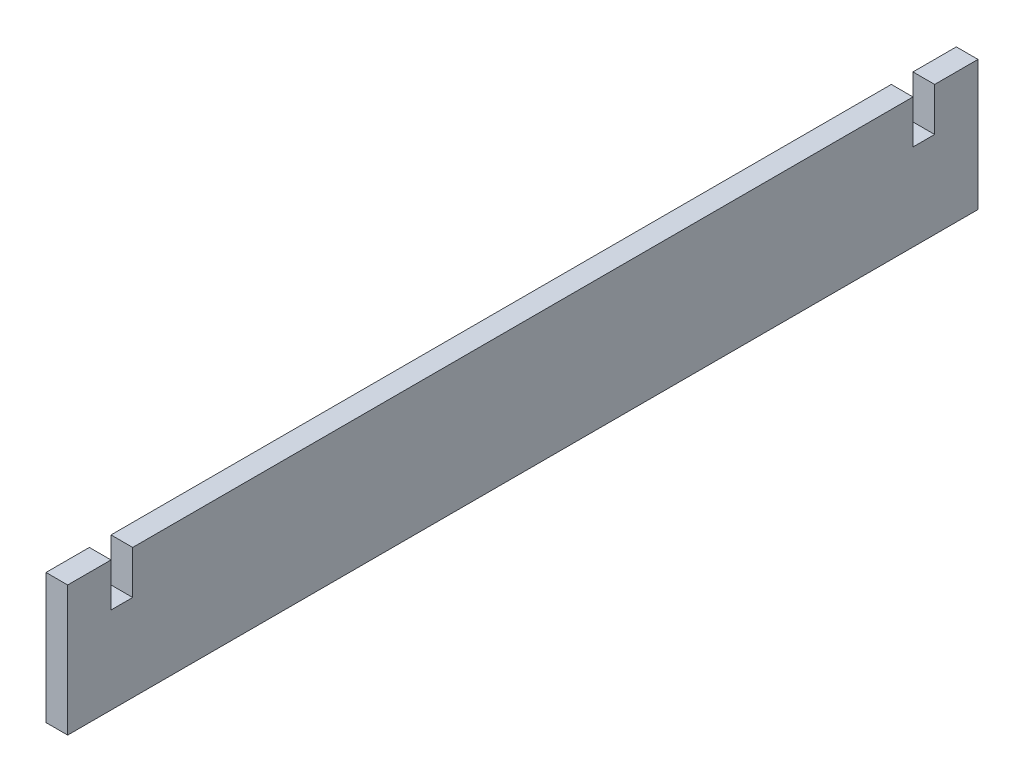
SolidWorks part; units mm, degrees
material "PE High Density"
ref_plane "Front Plane" through (0, 0, 0) normal (0, 0, 1) x (1, 0, 0)
ref_plane "Top Plane" through (0, 0, 0) normal (0, 1, 0) x (1, 0, 0)
ref_plane "Right Plane" through (0, 0, 0) normal (1, 0, 0) x (0, 0, -1)
sketch "Sketch1" plane through (0, 0, 0) normal (0, 0, 1) x (1, 0, 0)
  line L1 (-6.35, -38.1) -> (6.35, -38.1)
  line L2 (-6.35, -38.1) -> (-6.35, 38.1)
  line L3 (-6.35, 38.1) -> (6.35, 38.1)
  line L4 (6.35, -38.1) -> (6.35, 38.1)
  line L5 (-6.35, -38.1) -> (6.35, 38.1) construction
  line L6 (-6.35, 38.1) -> (6.35, -38.1) construction
  point P0 (0, 0)
  dimension "D1" = 12.7
  dimension "D2" = 76.2
extrude "Boss-Extrude1" add sketch "Sketch1" along normal blind 533.4
sketch "Sketch2" plane through (6.35, 0, 0) normal (1, 0, 0) x (0, 0, -1)
  line L0 (-533.4, 38.1) -> (0, 38.1) construction
  line L1 (-508, 38.1) -> (-495.3, 38.1)
  line L2 (-508, 38.1) -> (-508, 12.7)
  line L3 (-508, 12.7) -> (-495.3, 12.7)
  line L4 (-495.3, 38.1) -> (-495.3, 12.7)
  line L5 (-266.7, 38.1) -> (-266.7, -38.1) construction
  line L10 (-533.4, -38.1) -> (0, -38.1) construction
  line L11 (-38.1, 38.1) -> (-38.1, 12.7)
  line L12 (-25.4, 12.7) -> (-38.1, 12.7)
  line L13 (-25.4, 38.1) -> (-25.4, 12.7)
  line L14 (-25.4, 38.1) -> (-38.1, 38.1)
  line L15 (-533.4, -38.1) -> (-533.4, 38.1) construction
  dimension "D1" = 12.7
  dimension "D2" = 25.4
  dimension "D3" = 25.4
extrude "Cut-Extrude1" cut sketch "Sketch2" against normal through all
